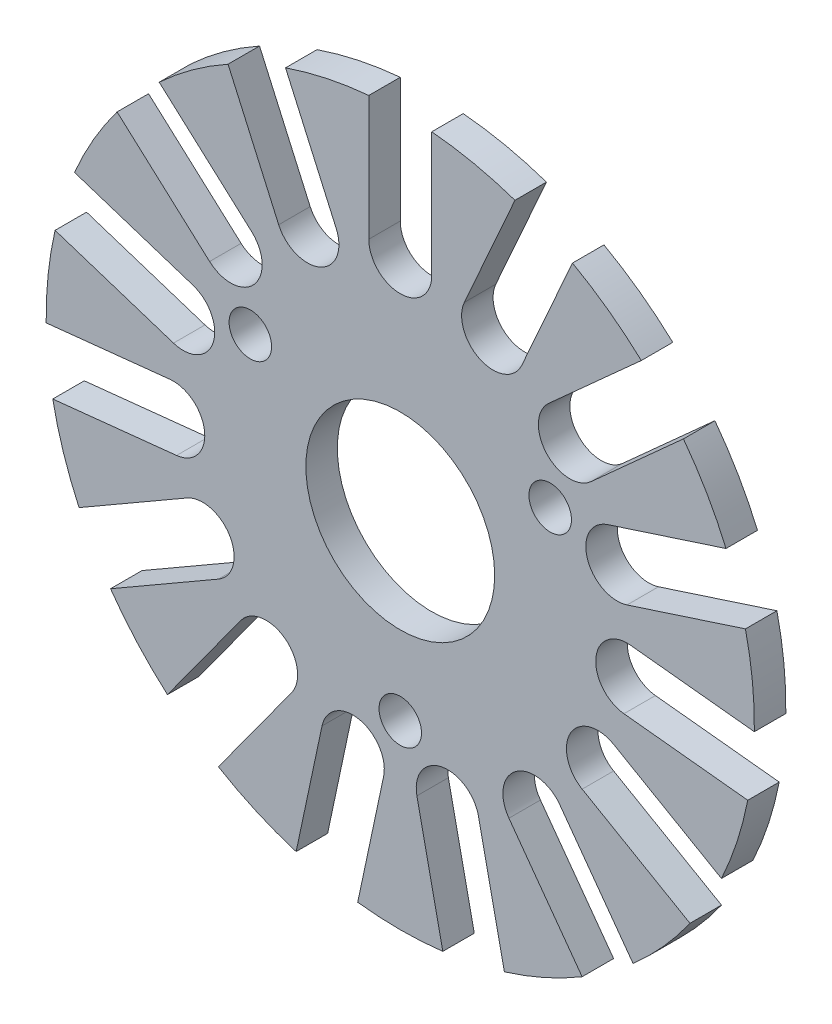
SolidWorks part; units mm, degrees
ref_plane "Front Plane" through (0, 0, 0) normal (0, 0, 1) x (1, 0, 0)
ref_plane "Top Plane" through (0, 0, 0) normal (0, 1, 0) x (1, 0, 0)
ref_plane "Right Plane" through (0, 0, 0) normal (1, 0, 0) x (0, 0, -1)
ref_plane "Plane1" through (0, 0, 0) normal (0, 0, -1) x (-1, 0, 0)
sketch "Sketch1" plane through (0, 0, 0) normal (0, 0, -1) x (-1, 0, 0)
  line L0 (-15.3163, 17.1022) -> (-9.4373, 11.8087)
  line L1 (-12.1139, 8.8361) -> (-17.9928, 14.1296)
  line L2 (-20.696, 9.4475) -> (-13.1723, 7.0029)
  line L3 (-14.4084, 3.1987) -> (-21.9321, 5.6433)
  line L4 (-22.4972, 0.2665) -> (-14.6296, 1.0934)
  line L5 (-14.2115, -2.8847) -> (-22.0791, -3.7116)
  line L6 (-20.4084, -8.8534) -> (-13.5574, -4.8979)
  line L7 (-11.5574, -8.362) -> (-18.4084, -12.3175)
  line L8 (-14.7909, -16.3352) -> (-10.1409, -9.9352)
  line L9 (-6.9049, -12.2863) -> (-11.5548, -18.6864)
  line L10 (-6.6158, -20.8854) -> (-4.971, -13.1473)
  line L11 (-1.0584, -13.9789) -> (-2.7032, -21.717)
  line L12 (2.7032, -21.717) -> (1.0584, -13.9789)
  line L13 (4.971, -13.1473) -> (6.6158, -20.8854)
  line L14 (11.5548, -18.6864) -> (6.9049, -12.2863)
  line L15 (10.1409, -9.9352) -> (14.7909, -16.3352)
  line L16 (18.4084, -12.3175) -> (11.5574, -8.362)
  line L17 (13.5574, -4.8979) -> (20.4084, -8.8534)
  line L18 (22.0791, -3.7116) -> (14.2115, -2.8847)
  line L19 (14.6296, 1.0934) -> (22.4972, 0.2665)
  line L20 (21.9321, 5.6433) -> (14.4084, 3.1987)
  line L21 (13.1723, 7.0029) -> (20.696, 9.4475)
  line L22 (17.9928, 14.1296) -> (12.1139, 8.8361)
  line L23 (9.4373, 11.8087) -> (15.3163, 17.1022)
  line L24 (10.9424, 20.28) -> (7.7248, 13.053)
  line L25 (4.0706, 14.6799) -> (7.2883, 21.9069)
  line L26 (2, 23.031) -> (2, 15.12)
  line L27 (-2, 15.12) -> (-2, 23.031)
  line L28 (-7.2883, 21.9069) -> (-4.0706, 14.6799)
  line L29 (-7.7248, 13.053) -> (-10.9424, 20.28)
  circle A0 centre (9.5263, 6.12) radius 1.35
  circle A1 centre (-9.5263, 6.12) radius 1.35
  circle A2 centre (0, -10.38) radius 1.35
  circle A3 centre (0, 0.62) radius 6
  arc A4 (-9.4373, 11.8087) -> (-12.1139, 8.8361) centre (-10.7756, 10.3224) cw
  arc A5 (-17.9928, 14.1296) -> (-20.696, 9.4475) centre (0, 0.62) ccw
  arc A6 (-13.1723, 7.0029) -> (-14.4084, 3.1987) centre (-13.7903, 5.1008) cw
  arc A7 (-21.9321, 5.6433) -> (-22.4972, 0.2665) centre (0, 0.62) ccw
  arc A8 (-14.6296, 1.0934) -> (-14.2115, -2.8847) centre (-14.4206, -0.8956) cw
  arc A9 (-22.0791, -3.7116) -> (-20.4084, -8.8534) centre (0, 0.62) ccw
  arc A10 (-13.5574, -4.8979) -> (-11.5574, -8.362) centre (-12.5574, -6.63) cw
  arc A11 (-18.4084, -12.3175) -> (-14.7909, -16.3352) centre (0, 0.62) ccw
  arc A12 (-10.1409, -9.9352) -> (-6.9049, -12.2863) centre (-8.5229, -11.1107) cw
  arc A13 (-11.5548, -18.6864) -> (-6.6158, -20.8854) centre (0, 0.62) ccw
  arc A14 (-4.971, -13.1473) -> (-1.0584, -13.9789) centre (-3.0147, -13.5631) cw
  arc A15 (-2.7032, -21.717) -> (2.7032, -21.717) centre (0, 0.62) ccw
  arc A16 (1.0584, -13.9789) -> (4.971, -13.1473) centre (3.0147, -13.5631) cw
  arc A17 (6.6158, -20.8854) -> (11.5548, -18.6864) centre (0, 0.62) ccw
  arc A18 (6.9049, -12.2863) -> (10.1409, -9.9352) centre (8.5229, -11.1107) cw
  arc A19 (14.7909, -16.3352) -> (18.4084, -12.3175) centre (0, 0.62) ccw
  arc A20 (11.5574, -8.362) -> (13.5574, -4.8979) centre (12.5574, -6.63) cw
  arc A21 (20.4084, -8.8534) -> (22.0791, -3.7116) centre (0, 0.62) ccw
  arc A22 (14.2115, -2.8847) -> (14.6296, 1.0934) centre (14.4206, -0.8956) cw
  arc A23 (22.4972, 0.2665) -> (21.9321, 5.6433) centre (0, 0.62) ccw
  arc A24 (14.4084, 3.1987) -> (13.1723, 7.0029) centre (13.7903, 5.1008) cw
  arc A25 (20.696, 9.4475) -> (17.9928, 14.1296) centre (0, 0.62) ccw
  arc A26 (12.1139, 8.8361) -> (9.4373, 11.8087) centre (10.7756, 10.3224) cw
  arc A27 (15.3163, 17.1022) -> (10.9424, 20.28) centre (0, 0.62) ccw
  arc A28 (7.7248, 13.053) -> (4.0706, 14.6799) centre (5.8977, 13.8664) cw
  arc A29 (7.2883, 21.9069) -> (2, 23.031) centre (0, 0.62) ccw
  arc A30 (2, 15.12) -> (-2, 15.12) centre (0, 15.12) cw
  arc A31 (-2, 23.031) -> (-7.2883, 21.9069) centre (0, 0.62) ccw
  arc A32 (-4.0706, 14.6799) -> (-7.7248, 13.053) centre (-5.8977, 13.8664) cw
  arc A33 (-10.9424, 20.28) -> (-15.3163, 17.1022) centre (0, 0.62) ccw
extrude "Boss-Extrude1" add sketch "Sketch1" against normal blind 2
